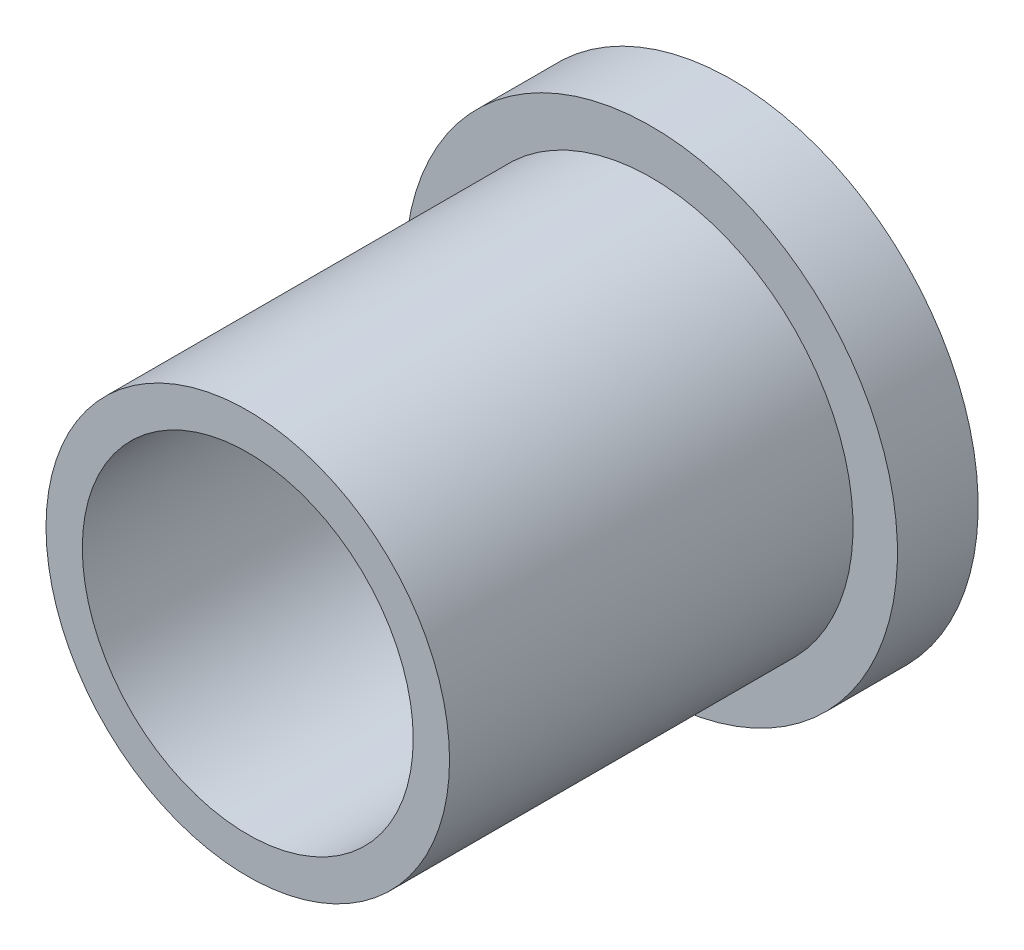
SolidWorks part; units mm, degrees
material "Silicon Rubber"
ref_plane "Front Plane" through (0, 0, 0) normal (0, 0, 1) x (1, 0, 0)
ref_plane "Top Plane" through (0, 0, 0) normal (0, 1, 0) x (1, 0, 0)
ref_plane "Right Plane" through (0, 0, 0) normal (1, 0, 0) x (0, 0, -1)
sketch "Sketch1" plane through (0, 0, 0) normal (0, 0, 1) x (1, 0, 0)
  circle A0 centre (0, 0) radius 5
  circle A1 centre (0, 0) radius 4.1
  dimension "D1" = 10
  dimension "D2" = 8.2
extrude "Boss-Extrude1" add sketch "Sketch1" along normal blind 10
sketch "Sketch2" plane through (0, 0, 0) normal (0, 0, -1) x (-1, 0, 0)
  circle A0 centre (0, 0) radius 4.1
extrude "Extrude-Thin1" add sketch "Sketch2" along normal blind 2 thin
